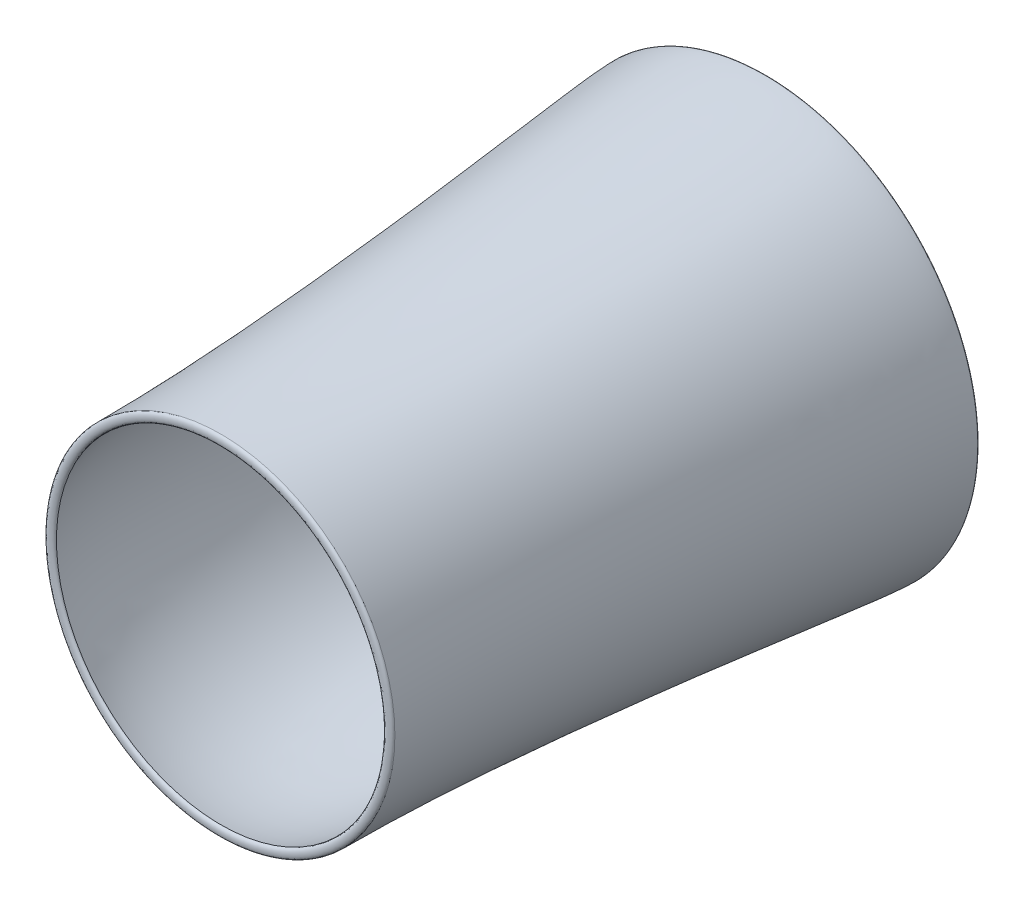
SolidWorks part; units mm, degrees
ref_plane "Front Plane" through (0, 0, 0) normal (0, 0, 1) x (1, 0, 0)
ref_plane "Top Plane" through (0, 0, 0) normal (0, 1, 0) x (1, 0, 0)
ref_plane "Right Plane" through (0, 0, 0) normal (1, 0, 0) x (0, 0, -1)
sketch "Sketch1" plane through (0, 0, 0) normal (0, 0, 1) x (1, 0, 0)
  circle A0 centre (0, 0) radius 50.8
  dimension "D1" = 101.6
ref_plane "Plane1" through (0, -254, 0) normal (0, 1, 0) x (1, 0, 0)
sketch "Sketch6" plane through (0, 0, 0) normal (0, 1, 0) x (1, 0, 0)
  line L0 (0, -99.6848) -> (0, 145.6048) construction
ref_plane "Plane2" through (0, -114.3, 0) normal (0, 1, 0) x (1, 0, 0)
sketch "Sketch12" plane through (0, 0, 0) normal (0, 1, 0) x (1, 0, 0)
  line L0 (0, -1104.7568) -> (0, -908.6135) construction
ref_plane "Plane3" through (0, 0, 203.2) normal (0, 0, 1) x (1, 0, 0)
ref_plane "Plane4" through (0, 0, 889) normal (0, 0, 1) x (1, 0, 0)
sketch "Sketch17" plane through (0, 0, 0) normal (0, 1, 0) x (1, 0, 0)
  line L0 (-259.4955, -43.5301) -> (-259.4955, 70.1436) construction
  line L1 (-110.6437, -1316.1124) -> (-110.6437, -853.5386) construction
  line L2 (-259.4955, 45.4622) -> (-387.328, 45.4622)
  line L3 (-387.328, 45.4622) -> (-387.328, -1084.8928)
  line L4 (-387.328, -1084.8928) -> (-110.6437, -1084.8928)
  spline S0 degree 3 poles (-259.4955, 45.4622) (-259.4955, -7.1736) (-207.7477, -105.8122) (-173.3147, -383.1384) (-92.4228, -818.9689) (-110.6437, -795.7842) (-110.6437, -1084.8928) knots 0 0 0 0 0.158009 0.206507 0.484977 1 1 1 1
sketch "Sketch21" plane through (0, 0, 0) normal (0, 1, 0) x (1, 0, 0)
  line L0 (-711.6099, -22.8536) -> (-711.6099, 113.778) construction
  line L1 (-581.9466, -1315.9117) -> (-581.9466, -853.874) construction
  line L2 (-535.7653, -15.554) -> (-711.6099, -15.554) construction
  line L3 (-549.9375, -1834.6416) -> (-581.9466, -1834.6416) construction
  line L4 (-549.9375, -1834.6416) -> (-581.9466, -1834.6416)
  line L6 (-535.7653, -15.554) -> (-711.6099, -15.554)
  spline S0 degree 3 poles (-535.7653, -15.554) (-621.6881, -211.8838) (-472.6325, -729.0649) (-643.2545, -1479.8166) (-549.9375, -1834.6416) knots 0 0 0 0 0.206507 1 1 1 1
  spline S1 degree 3 poles (-711.6099, -15.554) (-711.6099, -140.9379) (-581.9466, -1104.3325) (-581.9466, -1834.6416) knots 0 0 0 0 1 1 1 1
  point P10 (-432.3956, -1137.7564)
  point P11 (-356.3475, -332.2391)
  point P12 (-262.453, -580.6284)
  point P13 (-581.9466, -175.3008)
  point P14 (-581.9466, -1739.1054)
  point P15 (-362.686, -497.233)
  point P16 (-396.866, -1025.1237)
  point P17 (0, 0)
  point P18 (-450.0349, -952.966)
  point P19 (-581.9466, -383.2998)
  point P20 (-560.1703, -945.3705)
  point P21 (-549.9375, -1834.6416)
revolve "Revolve2" add sketch "Sketch21" angle 360 about L0
sketch "Sketch22" plane through (0, 0, 0) normal (0, 1, 0) x (1, 0, 0)
  line L0 (-711.6099, -15.554) -> (-535.7653, -15.554)
  line L1 (-535.7653, -19.363) -> (-535.7653, -11.7449) construction
  line L2 (-711.6099, -14.1612) -> (-711.6099, -16.9467) construction
  spline S0 degree 3 poles (-711.6099, -15.554) (-711.6099, 1.3794) (-535.7653, 1.3794) (-535.7653, -15.554) knots 0 0 0 0 1 1 1 1
revolve "Revolve3" add sketch "Sketch22" angle 360 about L0
sketch "Sketch23" plane through (0, 0, 0) normal (0, 1, 0) x (1, 0, 0)
  line L0 (-581.9466, -1834.6416) -> (-549.9375, -1834.6416)
  line L1 (-581.9466, -1843.8527) -> (-581.9466, -1825.4306) construction
  line L2 (-549.9375, -1824.0686) -> (-549.9375, -1845.2146) construction
  spline S0 degree 3 poles (-581.9466, -1834.6416) (-581.9466, -1847.3416) (-549.9375, -1847.3416) (-549.9375, -1834.6416) knots 0 0 0 0 1 1 1 1
revolve "Revolve4" add sketch "Sketch23" angle 360 about L0
ref_plane "Plane5" through (289.9098, 0, 0) normal (1, 0, 0) x (0, 0, -1)
sketch "Sketch24" plane through (289.9098, 0, 0) normal (1, 0, 0) x (0, 0, -1)
  line L0 (-1123.5724, -17.6357) -> (119.2276, -17.6357) construction
  line L1 (-1834.6416, 0) -> (-15.554, 0) construction
  line L2 (-1834.6416, -581.9466) -> (-1834.6416, 581.9466) construction
  line L3 (-15.554, 711.6099) -> (-15.554, -711.6099) construction
  text T0 "MD-130 Gas Turbine Engine" font "TI-Nspire" height in points 160
